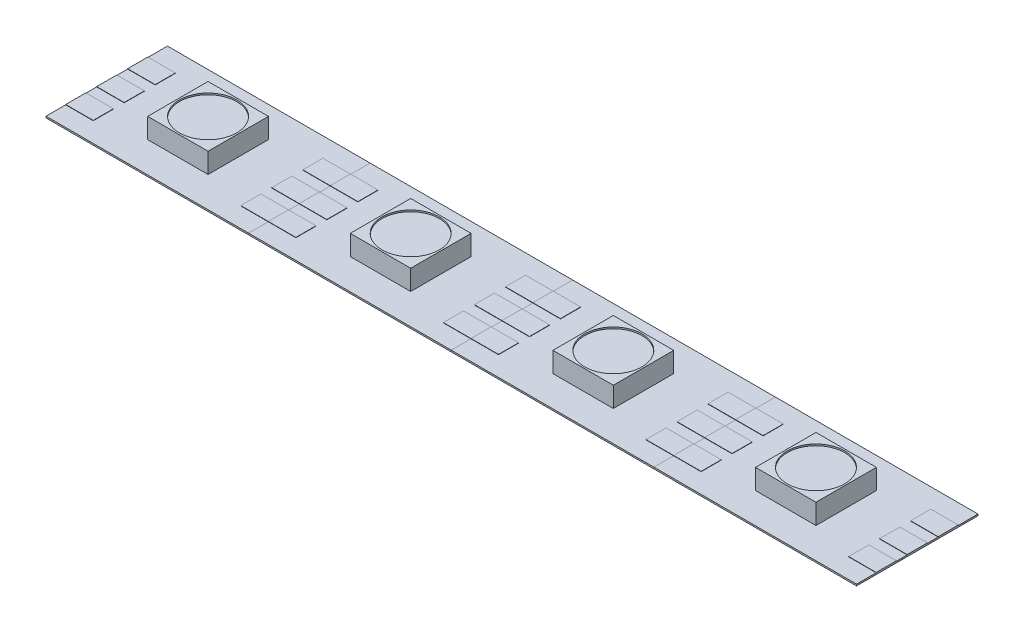
SolidWorks part; units mm, degrees
ref_plane "Front Plane" through (0, 0, 0) normal (0, 0, 1) x (1, 0, 0)
ref_plane "Top Plane" through (0, 0, 0) normal (0, 1, 0) x (1, 0, 0)
ref_plane "Right Plane" through (0, 0, 0) normal (1, 0, 0) x (0, 0, -1)
sketch "Sketch1" plane through (0, 0, 0) normal (0, 1, 0) x (1, 0, 0)
  line L0 (-8.3058, 4.9784) -> (8.3058, -4.9784) construction
  line L1 (-8.3058, 4.9784) -> (8.3058, 4.9784)
  line L2 (-8.3058, 4.9784) -> (-8.3058, -4.9784)
  line L3 (-8.3058, -4.9784) -> (8.3058, -4.9784)
  line L4 (8.3058, 4.9784) -> (8.3058, -4.9784)
  dimension "D1" = 9.9568
  dimension "D2" = 16.6116
extrude "Boss-Extrude1" add sketch "Sketch1" along normal blind 0.127
sketch "Sketch3" plane through (0, 0.127, 0) normal (0, 1, 0) x (1, 0, 0)
  line L0 (-8.3058, 4.9784) -> (8.3058, -4.9784) construction
  line L1 (-2.4765, 2.4765) -> (2.4765, -2.4765) construction
  line L2 (-2.4765, 2.4765) -> (2.4765, 2.4765)
  line L3 (-2.4765, 2.4765) -> (-2.4765, -2.4765)
  line L4 (-2.4765, -2.4765) -> (2.4765, -2.4765)
  line L5 (2.4765, 2.4765) -> (2.4765, -2.4765)
  dimension "D1" = 4.953
extrude "Boss-Extrude3" add sketch "Sketch3" along normal blind 1.651
sketch "Sketch4" plane through (0, 0.127, 0) normal (0, 1, 0) x (1, 0, 0)
  line L0 (-8.3058, 0) -> (8.3058, 0) construction
  line L1 (-8.3058, 4.9784) -> (-8.3058, -4.9784) construction
  line L2 (8.3058, -4.9784) -> (8.3058, 4.9784) construction
  line L3 (-6.047, 0) -> (-8.3058, 0) construction
  line L4 (-8.3058, 0.8255) -> (-6.047, 0.8255)
  line L5 (-8.3058, 0.8255) -> (-8.3058, -0.8255)
  line L6 (-8.3058, -0.8255) -> (-6.047, -0.8255)
  line L7 (-6.047, 0.8255) -> (-6.047, -0.8255)
  line L8 (-8.3058, 3.3655) -> (-6.047, 3.3655)
  line L9 (-6.047, 3.3655) -> (-6.047, 1.7145)
  line L10 (-8.3058, 1.7145) -> (-6.047, 1.7145)
  line L11 (-8.3058, 3.3655) -> (-8.3058, 1.7145)
  line L12 (-6.047, -3.3655) -> (-6.047, -1.7145)
  line L13 (-8.3058, -1.7145) -> (-6.047, -1.7145)
  line L14 (-8.3058, -3.3655) -> (-8.3058, -1.7145)
  line L15 (-8.3058, -3.3655) -> (-6.047, -3.3655)
  line L16 (0, 0) -> (0, -4.9784) construction
  line L17 (-8.3058, -4.9784) -> (8.3058, -4.9784) construction
  line L18 (8.3058, -3.3655) -> (8.3058, -1.7145)
  line L19 (8.3058, -3.3655) -> (6.047, -3.3655)
  line L20 (6.047, -3.3655) -> (6.047, -1.7145)
  line L21 (8.3058, -1.7145) -> (6.047, -1.7145)
  line L22 (8.3058, 0.8255) -> (8.3058, -0.8255)
  line L23 (8.3058, -0.8255) -> (6.047, -0.8255)
  line L24 (6.047, 0.8255) -> (6.047, -0.8255)
  line L25 (8.3058, 0.8255) -> (6.047, 0.8255)
  line L26 (8.3058, 1.7145) -> (6.047, 1.7145)
  line L27 (6.047, 3.3655) -> (6.047, 1.7145)
  line L28 (8.3058, 3.3655) -> (8.3058, 1.7145)
  line L29 (8.3058, 3.3655) -> (6.047, 3.3655)
  dimension "D1" = 1.651
  dimension "D2" = 2
extrude "Boss-Extrude4" add sketch "Sketch4" along normal blind 0.0254
sketch "Sketch5" plane through (0, 1.778, 0) normal (0, 1, 0) x (1, 0, 0)
  circle A0 centre (0, 0) radius 2.3483
extrude "Cut-Extrude1" cut sketch "Sketch5" against normal blind 0.127
pattern_linear "LPattern1" count 4 spacing 16.6116 along (1, 0, 0) of "Boss-Extrude3", "Boss-Extrude4", "Cut-Extrude1", "Boss-Extrude1"
